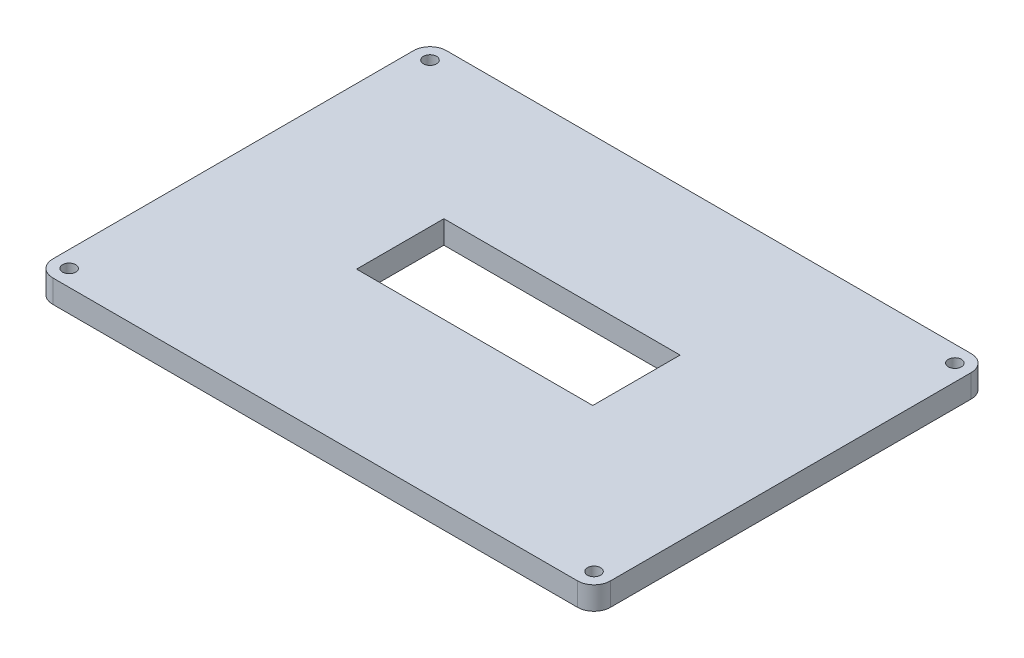
SolidWorks part; units mm, degrees
ref_plane "Front Plane" through (0, 0, 0) normal (0, 0, 1) x (1, 0, 0)
ref_plane "Top Plane" through (0, 0, 0) normal (0, 1, 0) x (1, 0, 0)
ref_plane "Right Plane" through (0, 0, 0) normal (1, 0, 0) x (0, 0, -1)
sketch "Sketch1" plane through (0, 0, 0) normal (0, 1, 0) x (1, 0, 0)
  line L1 (85, -60) -> (-85, -60)
  line L2 (85, -60) -> (85, 60)
  line L3 (85, 60) -> (-85, 60)
  line L4 (-85, -60) -> (-85, 60)
  line L5 (85, -60) -> (-85, 60) construction
  line L6 (85, 60) -> (-85, -60) construction
  point P0 (0, 0)
  dimension "D1" = 170
  dimension "D2" = 120
extrude "Boss-Extrude1" add sketch "Sketch1" along normal blind 7
sketch "Sketch2" plane through (0, 7, 0) normal (0, 1, 0) x (1, 0, 0)
  line L1 (-36, 15.2368) -> (36, 15.2368)
  line L2 (-36, 15.2368) -> (-36, -11.3838)
  line L3 (-36, -11.3838) -> (36, -11.3838)
  line L4 (36, 15.2368) -> (36, -11.3838)
  line L5 (-36, 15.2368) -> (36, -11.3838) construction
  line L6 (-36, -11.3838) -> (36, 15.2368) construction
  point P0 (0, 1.9265)
  dimension "D1" = 72
  dimension "D2" = 26.6206
extrude "Cut-Extrude1" cut sketch "Sketch2" against normal blind 7
sketch "Sketch3" plane through (0, 7, 0) normal (0, 1, 0) x (1, 0, 0)
  line L1 (85, 60) -> (-85, 60) construction
  line L2 (-85, 60) -> (-85, -60) construction
  circle A0 centre (-80, 55) radius 2
  circle A1 centre (-70, -45.36) radius 2
  dimension "D1" = 5
  dimension "D3" = 4
  dimension "D4" = 4
  dimension "D2" = 120
  dimension "D5" = 5
sketch "Sketch6" plane through (0, 7, 0) normal (0, 1, 0) x (1, 0, 0)
  line L0 (85, -60) -> (85, 60) construction
  line L1 (-85, -60) -> (85, -60) construction
  line L2 (85, 60) -> (-85, 60) construction
  circle A0 centre (80, -55) radius 2
  circle A1 centre (80, 55) radius 2
  dimension "D1" = 5
  dimension "D2" = 5
  dimension "D3" = 5
  dimension "D4" = 5
extrude "Cut-Extrude5" cut sketch "Sketch3" against normal blind 7 contours A0
sketch "Sketch7" plane through (0, 7, 0) normal (0, 1, 0) x (1, 0, 0)
  line L0 (-85, -60) -> (85, -60) construction
  line L1 (-85, 60) -> (-85, -60) construction
  circle A0 centre (-80, -55) radius 2
  dimension "D1" = 5
  dimension "D2" = 5
extrude "Cut-Extrude7" cut sketch "Sketch7" against normal blind 10
extrude "Cut-Extrude10" cut sketch "Sketch6" against normal blind 10 contours A1
sketch "Sketch9" plane through (0, 7, 0) normal (0, 1, 0) x (1, 0, 0)
  line L0 (85, -60) -> (85, 60) construction
  line L1 (-85, -60) -> (85, -60) construction
  circle A0 centre (80, -55) radius 2
  dimension "D1" = 5
  dimension "D2" = 5
extrude "Cut-Extrude11" cut sketch "Sketch9" against normal blind 10
fillet "Fillet1" radius 5 4 edges at (85, 3.5, -60) (85, 3.5, 60) (-85, 3.5, 60) (-85, 3.5, -60)
